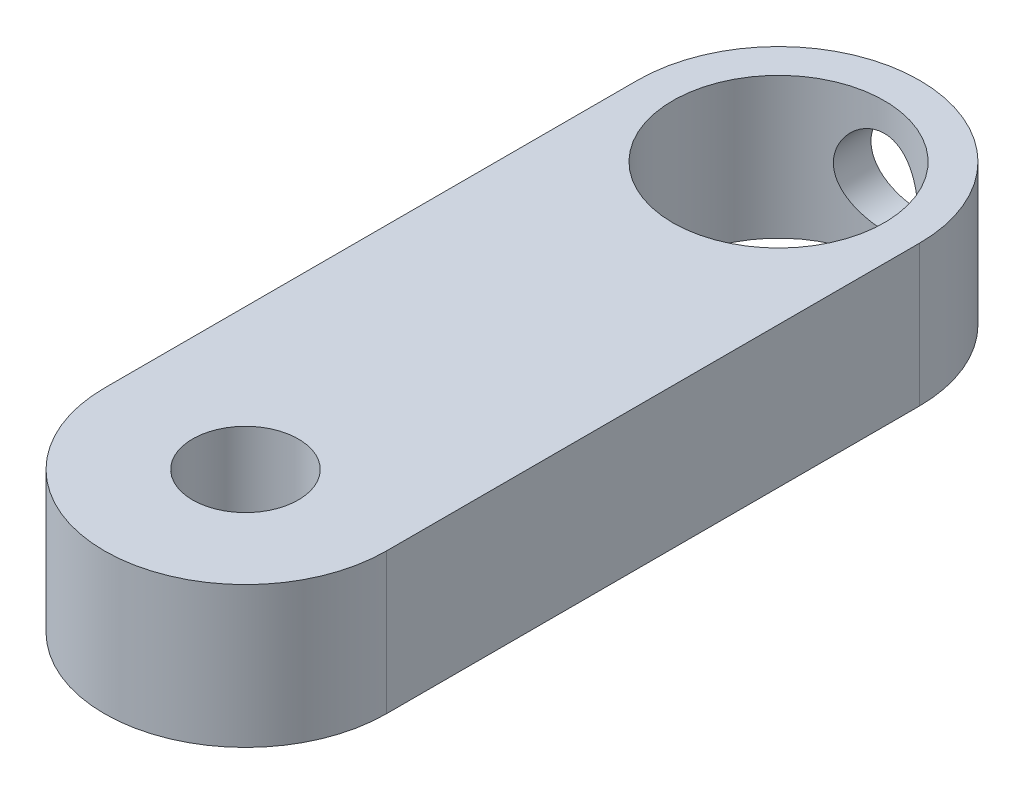
SolidWorks part; units mm, degrees
ref_plane "Front" through (0, 0, 0) normal (0, 0, 1) x (1, 0, 0)
ref_plane "Top" through (0, 0, 0) normal (0, 1, 0) x (1, 0, 0)
ref_plane "Right" through (0, 0, 0) normal (1, 0, 0) x (0, 0, -1)
sketch "Sketch1" plane through (0, 0, 0) normal (0, 1, 0) x (1, 0, 0)
  line L0 (0, 24) -> (0, 0) construction
  line L1 (6.35, 24) -> (6.35, 0)
  line L2 (-6.35, 24) -> (-6.35, 0)
  circle A1 centre (0, 24) radius 4.7625
  arc A2 (6.35, 24) -> (-6.35, 24) centre (0, 24) ccw
  arc A3 (-6.35, 0) -> (6.35, 0) centre (0, 0) ccw
  point P5 (0, 12)
  dimension "D3" = 6.35
  dimension "D4" = 9.525
  dimension "D1" = 24
extrude "Boss-Extrude1" add sketch "Sketch1" along normal blind 6.35
hole_wizard "3/16 (0.1875) Diameter Hole1" positions "Sketch6" profile "Sketch7" hole size "3/16" standard "ANSI Inch" end condition through all
sketch "Sketch6" plane through (0, 6.35, 0) normal (0, 1, 0) x (1, 0, 0)
  point P0 (0, 0)
sketch "Sketch7" plane through (0, 6.35, 0) normal (1, 0, 0) x (0, 0, 1)
  line L0 (0, 0) -> (0, 6.35)
  line L1 (0, 6.35) -> (2.3812, 6.35)
  line L2 (2.3812, 6.35) -> (2.3812, 0)
  line L5 (2.3812, 0) -> (0, 0)
  line L11 (0, -6.35) -> (0, 107.95) construction
  dimension "Thru Hole Dia." = 4.7625
  dimension "Thru Hole Depth" = 6.35
ref_plane "Plane1" through (0, 0, -30.35) normal (0, 0, -1) x (-1, 0, 0)
hole_wizard "#6-32 Tapped Hole1" positions "Sketch8" profile "Sketch10" tap size "#6-32" standard "ANSI Inch"
sketch "Sketch8" plane through (0, 0, -30.35) normal (0, 0, -1) x (-1, 0, 0)
  line L0 (0, 0) -> (0, 6.35)
  line L1 (6.35, 6.35) -> (-6.35, 6.35) construction
  point P0 (0, 3.175)
  point P9 (0, 0)
  point P10 (0, 2.5156)
  point P11 (0, 3.175)
sketch "Sketch10" plane through (0, 3.175, -30.35) normal (1, 0, 0) x (0, 1, 0)
  line L0 (0, 0) -> (0, 23.1647)
  line L1 (0, 23.1647) -> (1.3525, 22.352)
  line L2 (1.3525, 22.352) -> (1.3525, 0)
  line L5 (1.3525, 0) -> (0, 0)
  line L10 (0, 23.1647) -> (-1.3526, 22.352) construction
  line L11 (0, -6.35) -> (0, 107.95) construction
  dimension "Tap Drill Dia." = 2.7051
  dimension "Tap Drill Depth" = 22.352
  dimension "Drill Angle" = 118
cosmetic thread "Hole Thread1" parameters "D1"=15.875, "D2"=3.5052
hole_wizard "#6 Clearance Hole1" positions "Sketch11" profile "Sketch12" hole size "#6" standard "ANSI Inch"
sketch "Sketch11" plane through (0, 0, -30.35) normal (0, 0, -1) x (-1, 0, 0)
  point P0 (0, 3.175)
sketch "Sketch12" plane through (0, 3.175, -30.35) normal (1, 0, 0) x (0, 1, 0)
  line L0 (0, 0) -> (0, 7.4908)
  line L1 (0, 7.4908) -> (1.8986, 6.35)
  line L2 (1.8986, 6.35) -> (1.8986, 0)
  line L5 (1.8986, 0) -> (0, 0)
  line L10 (0, 7.4908) -> (-1.8986, 6.35) construction
  line L11 (0, -6.35) -> (0, 107.95) construction
  dimension "Hole Dia." = 3.7973
  dimension "Hole Depth" = 6.35
  dimension "Drill Angle" = 118
